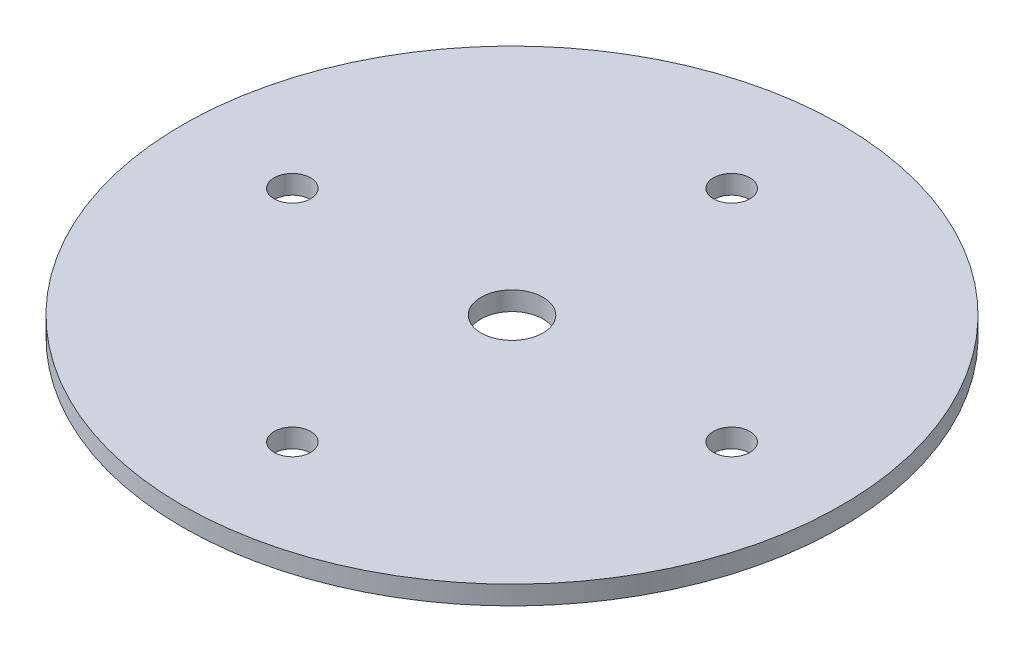
SolidWorks part; units mm, degrees
ref_plane "Front Plane" through (0, 0, 0) normal (0, 0, 1) x (1, 0, 0)
ref_plane "Top Plane" through (0, 0, 0) normal (0, 1, 0) x (1, 0, 0)
ref_plane "Right Plane" through (0, 0, 0) normal (1, 0, 0) x (0, 0, -1)
sketch "Sketch1" plane through (0, 0, 0) normal (0, 1, 0) x (1, 0, 0)
  line L0 (0, 32.025) -> (0, 4.925) construction
  circle A0 centre (0, 0) radius 4.925
  circle A1 centre (0, 0) radius 52.4
  circle A2 centre (0, 0) radius 34.925 construction
  circle A3 centre (0, 34.925) radius 2.9
  circle A4 centre (34.925, 0) radius 2.9
  circle A5 centre (0, -34.925) radius 2.9
  circle A6 centre (-34.925, 0) radius 2.9
  dimension "D1" = 5.8
  dimension "D2" = 9.85
  dimension "D4" = 104.8
  dimension "D3" = 27.1
extrude "Boss-Extrude1" add sketch "Sketch1" along normal blind 3
